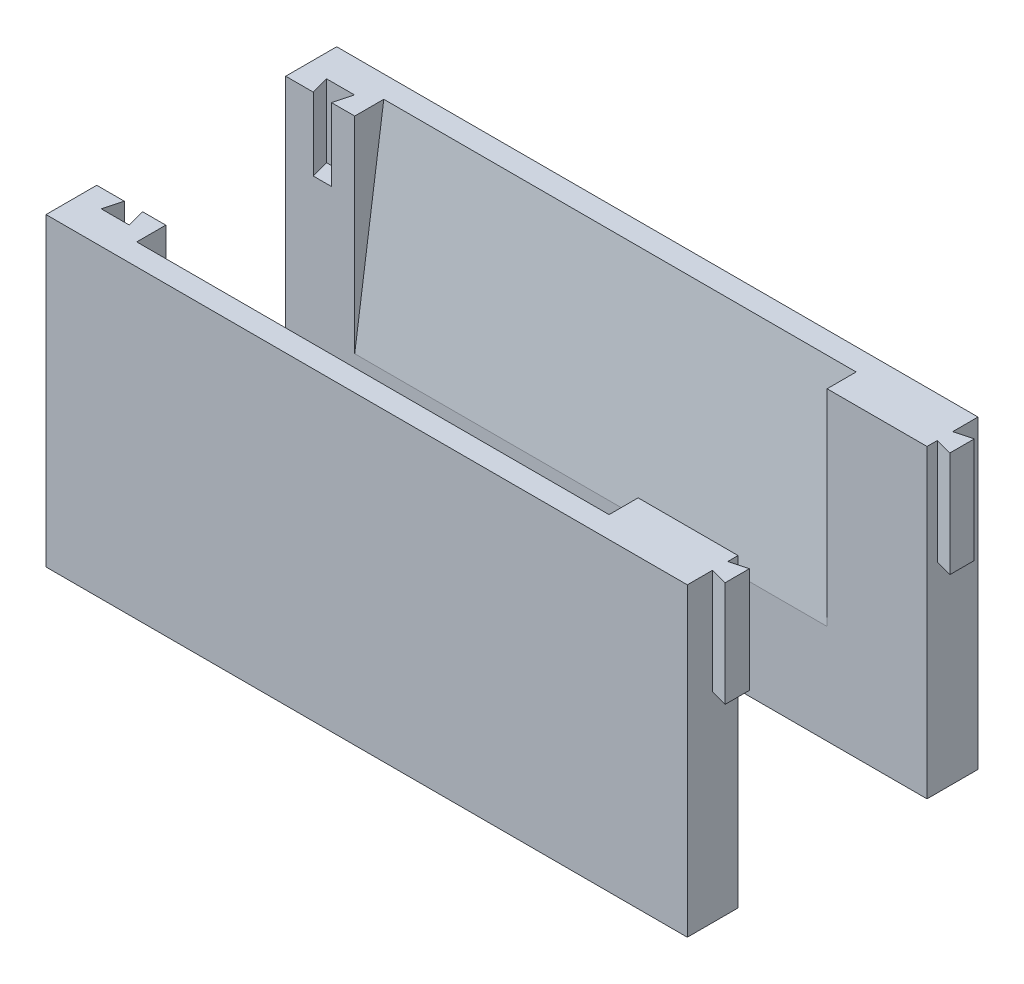
SolidWorks part; units mm, degrees
ref_plane "Front Plane" through (0, 0, 0) normal (0, 0, 1) x (1, 0, 0)
ref_plane "Top Plane" through (0, 0, 0) normal (0, 1, 0) x (1, 0, 0)
ref_plane "Right Plane" through (0, 0, 0) normal (1, 0, 0) x (0, 0, -1)
sketch "Sketch1" plane through (0, 0, 0) normal (0, 0, 1) x (1, 0, 0)
  line L1 (-41.951, 14.0483) -> (46.299, 14.0483)
  line L2 (-41.951, 14.0483) -> (-41.951, -27.9517)
  line L3 (-41.951, -27.9517) -> (46.299, -27.9517)
  line L4 (46.299, 14.0483) -> (46.299, -27.9517)
  dimension "D1" = 88.25
  dimension "D2" = 42
extrude "Boss-Extrude1" add sketch "Sketch1" along normal blind 5
sketch "Sketch2" plane through (0, 14.0483, 0) normal (0, 1, 0) x (1, 0, 0)
  line L0 (-41.951, 0) -> (-38.151, 0) construction
  line L1 (46.299, 0) -> (-41.951, 0) construction
  line L2 (-38.151, 0) -> (-38.8209, -2.5)
  line L3 (-38.8209, -2.5) -> (-34.9812, -2.5)
  line L4 (-34.9812, -2.5) -> (-35.651, 0)
  line L5 (-35.651, 0) -> (-34.6672, 0) construction
  dimension "D1" = 3.8
  dimension "D2" = 105
  dimension "D3" = 105
  dimension "D4" = 2.5
  dimension "D5" = 2.5
  dimension "D6" = 2.5
extrude "Cut-Extrude1" cut sketch "Sketch2" against normal blind 10 and the other way through all
sketch "Sketch3" plane through (0, 14.0483, 0) normal (0, 1, 0) x (1, 0, 0)
  line L0 (46.299, -5) -> (46.299, -3.52) construction
  line L1 (46.299, -5) -> (46.299, 0) construction
  line L2 (46.299, -3.52) -> (48.649, -4.1497)
  line L3 (48.649, -4.1497) -> (48.649, -0.7903)
  line L4 (48.649, -0.7903) -> (46.299, -1.42)
  line L5 (46.299, -1.42) -> (46.299, 0) construction
  line L6 (46.299, -1.42) -> (46.299, -3.52)
  dimension "D1" = 2.1
  dimension "D2" = 1.48
  dimension "D3" = 2.35
  dimension "D4" = 105
  dimension "D5" = 105
extrude "Boss-Extrude2" add sketch "Sketch3" against normal blind 14.5
ref_plane "Plane1" through (0, 0, -13) normal (0, 0, -1) x (-1, 0, 0)
ref_plane "Plane2" through (-32.451, 0, 0) normal (-1, 0, 0) x (0, 0, 1)
sketch "Sketch6" plane through (-32.451, 0, 0) normal (-1, 0, 0) x (0, 0, 1)
  line L1 (-0.05, 14.0483) -> (-0.05, -27.9517) construction
  line L3 (-0.05, -14.6296) -> (0, 14.0483)
  line L4 (0, 14.0483) -> (4, 14.0483)
  line L5 (5, 14.0483) -> (0, 14.0483) construction
  line L6 (4, 14.0483) -> (-0.05, -14.6296)
  dimension "D1" = 4
extrude "Cut-Extrude2" cut sketch "Sketch6" against normal blind 65
mirror "Mirror3" about plane through (0, 0, -13) normal (0, 0, -1) of bodies 106 102
sketch "Sketch7" plane through (0, 14.0483, 0) normal (0, 1, 0) x (1, 0, 0)
  line L0 (58.299, 33.0175) -> (46.299, 33.0175) construction
  line L1 (-41.951, -5) -> (46.299, -5)
  line L2 (-41.951, -5) -> (-41.951, -6.9825)
  line L3 (-41.951, -6.9825) -> (46.299, -6.9825)
  line L4 (46.299, -5) -> (46.299, -6.9825)
  line L5 (-41.951, 31) -> (46.299, 31)
  line L6 (-41.951, 31) -> (-41.951, 33.0175)
  line L7 (-41.951, 33.0175) -> (46.299, 33.0175)
  line L8 (46.299, 31) -> (46.299, 33.0175)
extrude "Boss-Extrude3" add sketch "Sketch7" against normal blind 42
